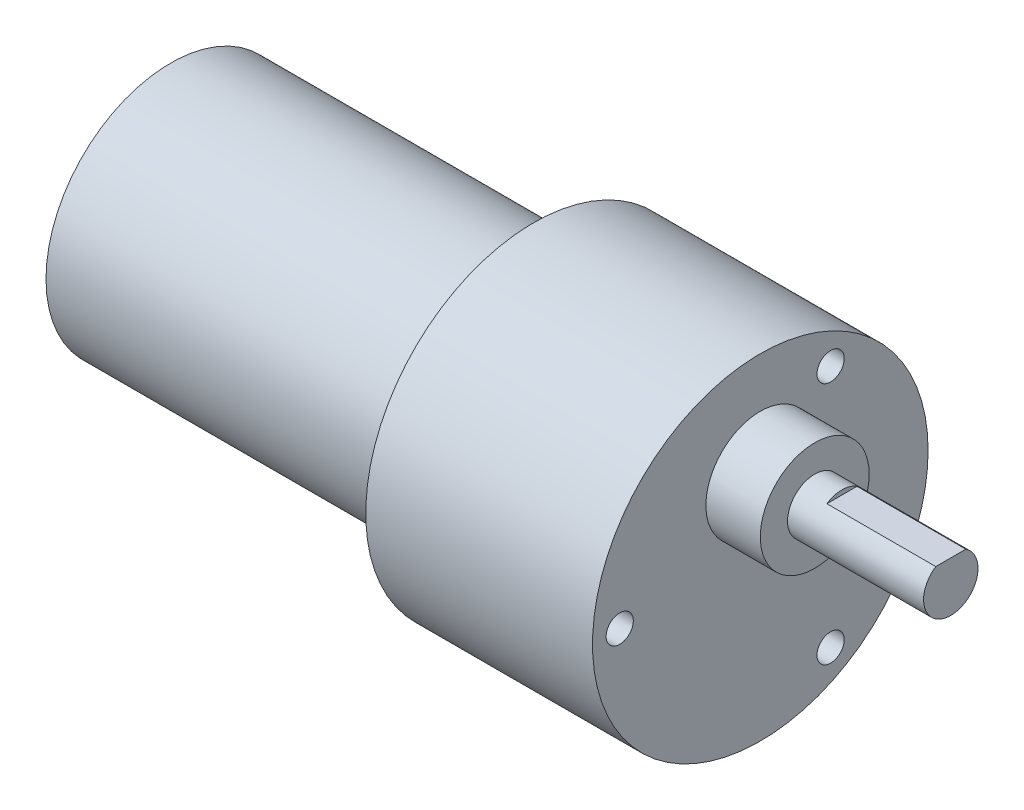
SolidWorks part; units mm, degrees
material "AISI 304"
ref_plane "正面" through (0, 0, 0) normal (0, 0, 1) x (1, 0, 0)
ref_plane "平面" through (0, 0, 0) normal (0, 1, 0) x (1, 0, 0)
ref_plane "右側面" through (0, 0, 0) normal (1, 0, 0) x (0, 0, -1)
sketch "ｽｹｯﾁ1" plane through (0, 0, 0) normal (1, 0, 0) x (0, 0, -1)
  circle A0 centre (0, 0) radius 13.75
  dimension "D1" = 27.5
extrude "ﾎﾞｽ - 押し出し1" add sketch "ｽｹｯﾁ1" along normal mid plane 40
sketch "ｽｹｯﾁ2" plane through (-20, 0, 0) normal (-1, 0, 0) x (0, 0, 1)
  circle A0 centre (0, 0) radius 5.1
  dimension "D1" = 10.2
extrude "ﾎﾞｽ - 押し出し2" add sketch "ｽｹｯﾁ2" along normal blind 3
sketch "ｽｹｯﾁ3" plane through (20, 0, 0) normal (1, 0, 0) x (0, 0, -1)
  circle A0 centre (0, 0) radius 18.5
  dimension "D1" = 37
extrude "ﾎﾞｽ - 押し出し3" add sketch "ｽｹｯﾁ3" along normal blind 25
sketch "ｽｹｯﾁ4" plane through (45, 0, 0) normal (1, 0, 0) x (0, 0, -1)
  circle A0 centre (0, 7) radius 6
  circle A1 centre (0, 0) radius 18.5 construction
  dimension "D1" = 12
  dimension "D2" = 7
extrude "ﾎﾞｽ - 押し出し4" add sketch "ｽｹｯﾁ4" along normal blind 6
sketch "ｽｹｯﾁ5" plane through (51, 0, 0) normal (1, 0, 0) x (0, 0, -1)
  circle A0 centre (0, 7) radius 3
  dimension "D1" = 6
extrude "ﾎﾞｽ - 押し出し5" add sketch "ｽｹｯﾁ5" along normal blind 15
sketch "ｽｹｯﾁ6" plane through (66, 0, 0) normal (1, 0, 0) x (0, 0, -1)
  line L0 (-1.6583, 9.5) -> (1.6583, 9.5)
  circle A1 centre (0, 7) radius 3 construction
  circle A2 centre (0, 7) radius 3
  circle M5 centre (0, 7) radius 3
  dimension "D1" = 2.5
extrude "ｶｯﾄ - 押し出し1" cut sketch "ｽｹｯﾁ6" against normal blind 12 contours L0 M5
sketch "ｽｹｯﾁ7" plane through (45, 0, 0) normal (1, 0, 0) x (0, 0, -1)
  circle A0 centre (-15.5, 0) radius 1.5
  circle A1 centre (0, 0) radius 18.5 construction
  circle A2 centre (7.75, 13.4234) radius 1.5
  circle A3 centre (7.75, -13.4234) radius 1.5
  dimension "D1" = 3
  dimension "D2" = 15.5
  dimension "D3" = 3
extrude "ｶｯﾄ - 押し出し2" cut sketch "ｽｹｯﾁ7" against normal blind 3
chamfer "面取り1" distance 2 angle 45 1 edges at (20, 0, -13.75)
